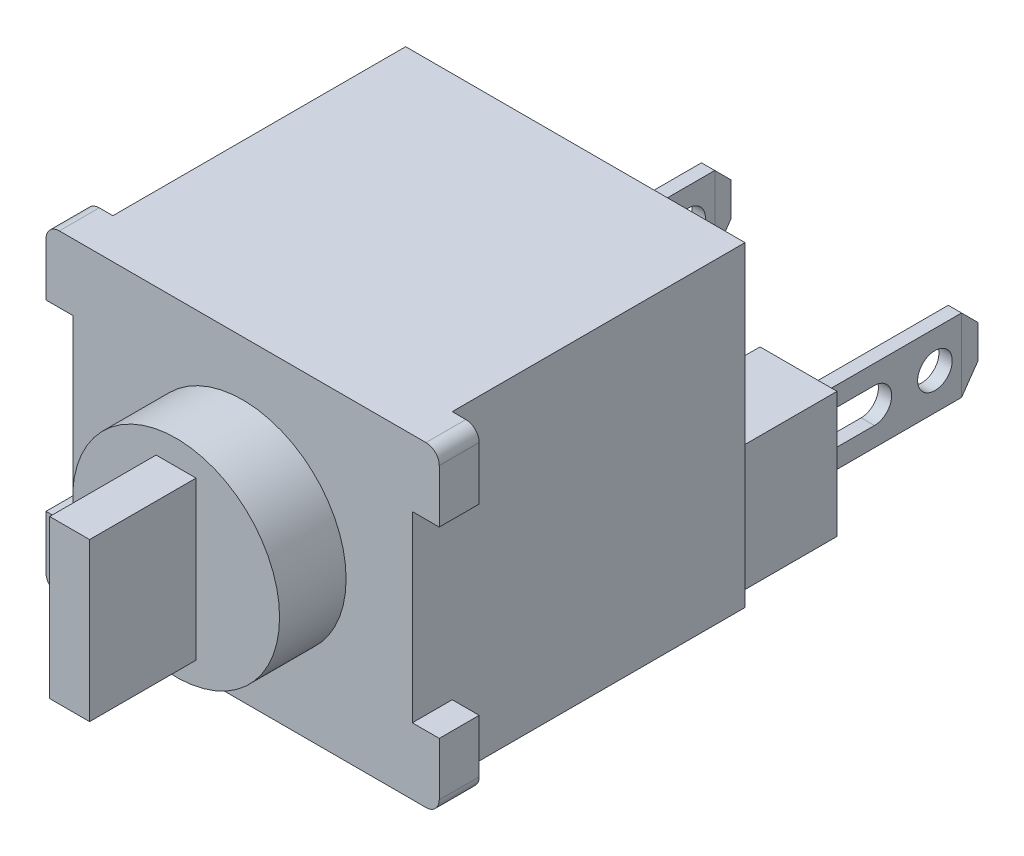
SolidWorks part; units mm, degrees
ref_plane "Front" through (0, 0, 0) normal (0, 0, 1) x (1, 0, 0)
ref_plane "Top" through (0, 0, 0) normal (0, 1, 0) x (1, 0, 0)
ref_plane "Right" through (0, 0, 0) normal (1, 0, 0) x (0, 0, -1)
sketch "Sketch1" plane through (0, 0, 0) normal (0, 0, 1) x (1, 0, 0)
  line L0 (0, 6.0325) -> (0, -6.0325) construction
  line L1 (-6.477, 6.0325) -> (6.477, 6.0325)
  line L2 (-6.477, 6.0325) -> (-6.477, -6.0325)
  line L3 (-6.477, -6.0325) -> (6.477, -6.0325)
  line L4 (6.477, 6.0325) -> (6.477, -6.0325)
  point P6 (0, 0)
  dimension "D1" = 12.954
  dimension "D2" = 12.065
extrude "Extrude1" add sketch "Sketch1" along normal blind 12.7
sketch "Sketch2" plane through (0, 0, 0) normal (0, 0, -1) x (-1, 0, 0)
  line L0 (0, 0) -> (0, -6.0325) construction
  line L1 (6.1799, -5.7354) -> (3.2407, -5.7354)
  line L2 (6.1799, -5.7354) -> (6.1799, -0.9373)
  line L3 (6.1799, -0.9373) -> (3.2407, -0.9373)
  line L4 (3.2407, -5.7354) -> (3.2407, -0.9373)
  line L5 (6.477, -6.0325) -> (-6.477, -6.0325) construction
  line L7 (6.1799, -5.7354) -> (6.1799, -6.0325) construction
  line L8 (6.1799, -5.7354) -> (6.477, -5.7354) construction
  line L9 (6.477, 6.0325) -> (6.477, -6.0325) construction
extrude "standoff" add sketch "Sketch2" along normal blind 3.81
sketch "Sketch3" plane through (0, 0, -3.81) normal (0, 0, -1) x (-1, 0, 0)
  line L0 (4.7103, -5.7354) -> (4.7103, -0.9373) construction
  line L1 (4.9643, -4.7333) -> (4.4563, -4.7333)
  line L2 (4.9643, -4.7333) -> (4.9643, -1.9393)
  line L3 (4.9643, -1.9393) -> (4.4563, -1.9393)
  line L4 (4.4563, -4.7333) -> (4.4563, -1.9393)
  line L5 (3.2407, -5.7354) -> (6.1799, -5.7354) construction
  line L6 (6.1799, -0.9373) -> (3.2407, -0.9373) construction
  line L7 (4.9643, -3.3363) -> (4.4563, -3.3363) construction
  point P12 (4.7103, -3.3363)
  dimension "D1" = 0.508
  dimension "D2" = 2.794
extrude "metal" add sketch "Sketch3" along normal blind 6.731
sketch "Sketch4" plane through (-4.9643, 0, 0) normal (-1, 0, 0) x (0, 0, 1)
  line L0 (-10.541, -3.3363) -> (-3.81, -3.3363) construction
  line L1 (-10.541, -4.7333) -> (-10.541, -1.9393) construction
  line L2 (-3.81, -4.7333) -> (-3.81, -1.9393) construction
  line L3 (-4.4704, -3.3363) -> (-6.4516, -3.3363) construction
  line L4 (-4.4704, -3.9967) -> (-6.4516, -3.9967)
  line L5 (-4.4704, -2.6759) -> (-6.4516, -2.6759)
  arc A0 (-4.4704, -3.9967) -> (-4.4704, -2.6759) centre (-4.4704, -3.3363) ccw
  arc A1 (-6.4516, -2.6759) -> (-6.4516, -3.9967) centre (-6.4516, -3.3363) ccw
  circle A2 centre (-8.763, -3.3363) radius 0.6604
  point P8 (-5.461, -3.3363)
  point P15 (-3.81, -3.3363)
  point P16 (-7.112, -3.3363)
  dimension "D1" = 0
  dimension "D3" = 1.778
  dimension "D4" = 1.3208
  dimension "D2" = 3.302
extrude "wire hole" cut sketch "Sketch4" against normal up to next
chamfer "Chamfer1" distance 0.762 angle 45 2 edges at (-4.7103, -4.7333, -10.541) (-4.7103, -1.9393, -10.541)
chamfer "Chamfer2" distance 0.762 angle 10 2 edges at (-4.4563, -3.3363, -10.541) (-4.9643, -3.3363, -10.541)
mirror "connector mirror" about plane through (0, 0, 0) normal (1, 0, 0) of "wire hole", "standoff", "metal", "Chamfer2", "Chamfer1"
sketch "Sketch5" plane through (0, 0, 12.7) normal (0, 0, 1) x (1, 0, 0)
  line L0 (-6.477, -6.0325) -> (6.477, -6.0325) construction
  line L1 (7.5057, 6.0325) -> (-7.5057, 6.0325)
  line L2 (7.5057, 6.0325) -> (7.5057, -6.0325)
  line L3 (7.5057, -6.0325) -> (-7.5057, -6.0325)
  line L4 (-7.5057, 6.0325) -> (-7.5057, -6.0325)
  line L5 (6.477, 6.0325) -> (-6.477, 6.0325) construction
  line L6 (0, -6.0325) -> (0, 6.0325) construction
  line L7 (7.5057, -3.4925) -> (-7.5057, -3.4925)
  line L9 (-7.5057, 3.4925) -> (7.5057, 3.4925)
  point P10 (0, 0)
  line M1 (-6.477, 6.0325) -> (-6.477, -6.0325)
  line M3 (6.477, -6.0325) -> (6.477, 6.0325)
  dimension "D1" = 2.54
  dimension "D2" = 15.0114
  dimension "D3" = 2.54
extrude "tabs" add sketch "Sketch5" against normal blind 1.524 contours L2 L7 L3 M3 | L9 L2 L1 M3 | L4 L9 L1 M1 | L7 L4 L3 M1
fillet "Fillet1" radius 0.508 4 edges at (-7.5057, -6.0325, 11.938) (-7.5057, 6.0325, 11.938) (7.5057, 6.0325, 11.938) (7.5057, -6.0325, 11.938)
sketch "Sketch6" plane through (0, 0, 0) normal (0, 0, -1) x (-1, 0, 0)
  text T0 "SANWA" font "Century Gothic" height 2.032
extrude "text" add sketch "Sketch6" along normal blind 0.254
sketch "Sketch7" plane through (0, 0, 12.7) normal (0, 0, 1) x (1, 0, 0)
  circle A0 centre (0, 0) radius 3.9497
  dimension "D1" = 7.8994
extrude "plunger" add sketch "Sketch7" along normal blind 2.54
sketch "Sketch8" plane through (0, 0, 15.24) normal (0, 0, 1) x (1, 0, 0)
  line L0 (0.762, 0) -> (-0.762, 0) construction
  line L1 (0.762, -3.0099) -> (-0.762, -3.0099)
  line L2 (0.762, -3.0099) -> (0.762, 3.0099)
  line L3 (0.762, 3.0099) -> (-0.762, 3.0099)
  line L4 (-0.762, -3.0099) -> (-0.762, 3.0099)
  point P6 (0, 0)
  dimension "D1" = 6.0198
  dimension "D2" = 1.524
extrude "plunger I" add sketch "Sketch8" along normal blind 4.064
